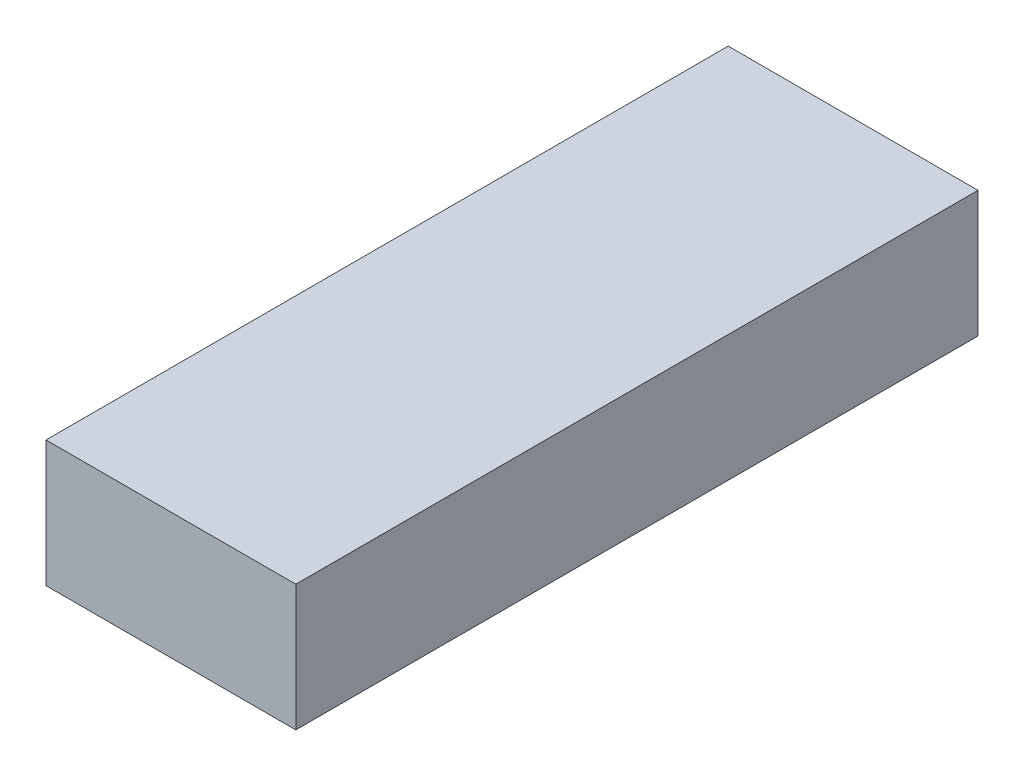
SolidWorks part; units mm, degrees
ref_plane "Front Plane" through (0, 0, 0) normal (0, 0, 1) x (1, 0, 0)
ref_plane "Top Plane" through (0, 0, 0) normal (0, 1, 0) x (1, 0, 0)
ref_plane "Right Plane" through (0, 0, 0) normal (1, 0, 0) x (0, 0, -1)
sketch "Sketch1" plane through (0, 0, 0) normal (0, 1, 0) x (1, 0, 0)
  line L0 (0, 0) -> (0, 71)
  line L1 (0, 71) -> (26, 71)
  line L2 (26, 71) -> (26, 0)
  line L3 (26, 0) -> (0, 0)
  dimension "D1" = 26
  dimension "D2" = 71
extrude "Boss-Extrude1" add sketch "Sketch1" along normal blind 13.1318
